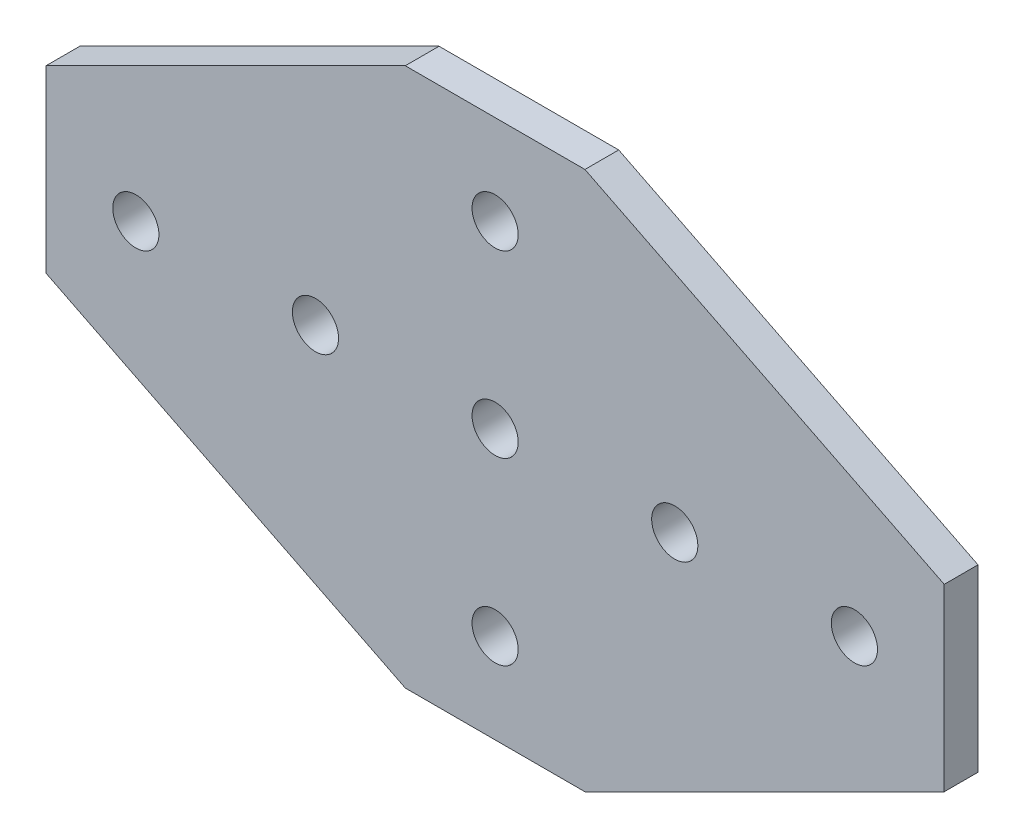
SolidWorks part; units mm, degrees
ref_plane "Front"
ref_plane "Top"
ref_plane "Right"
sketch "Sketch1" plane through (0, 0, 0) normal (0, 0, 1) x (1, 0, 0)
  line L0 (50.8, 0) -> (76.2, 0)
  line L1 (76.2, 0) -> (127, 25.4)
  line L2 (127, 25.4) -> (127, 50.8)
  line L3 (127, 50.8) -> (76.2, 76.2)
  line L4 (76.2, 76.2) -> (50.8, 76.2)
  line L5 (50.8, 76.2) -> (0, 50.8)
  line L6 (0, 50.8) -> (0, 25.4)
  line L7 (0, 25.4) -> (50.8, 0)
  line L8 (63.5, 76.2) -> (63.5, 0) construction
  line L9 (0, 38.1) -> (127, 38.1) construction
  dimension "WidthX" = 127
  dimension "HeightY" = 76.2
  dimension "CornerY" = 25.4
  dimension "CornerX" = 25.4
extrude "Base Extrude" add sketch "Sketch1" along normal blind 4.7752
sketch "Sketch2" plane through (0, 0, 4.7752) normal (0, 0, 1) x (1, 0, 0)
  line L0 (0, 50.8) -> (0, 25.4) construction
  line L1 (50.8, 0) -> (76.2, 0) construction
  circle A0 centre (12.7, 38.1) radius 3.2639
  dimension "Hole1Diam" = 6.5278
  dimension "Hole1X" = 12.7
  dimension "Hole1Y" = 38.1
extrude "Hole1" cut sketch "Sketch2" against normal through all
pattern_linear "Hole1 Pattern" count 5 spacing 25.4 along (1, 0, 0) of "Hole1"
sketch "Sketch3" plane through (0, 0, 4.7752) normal (0, 0, 1) x (1, 0, 0)
  line L0 (0, 50.8) -> (0, 25.4) construction
  line L1 (50.8, 0) -> (76.2, 0) construction
  circle A0 centre (63.5, 12.7) radius 3.2639
  dimension "Hole2Diam" = 6.5278
  dimension "Hole2X" = 63.5
  dimension "Hole2Y" = 12.7
extrude "Hole2" cut sketch "Sketch3" against normal through all
pattern_linear "Hole2 Pattern" count 2 spacing 50.8 along (0, 1, 0) count 2 spacing 50.8 along (0, 1, 0) of "Hole2"
ref_plane "Mate 1"
ref_plane "Mate 2"
ref_plane "Mate 3"
ref_plane "Mate 4"
ref_plane "Mate 5"
ref_plane "Mate 6"
ref_plane "Mate 7"
ref_plane "Mate 8"
ref_plane "Mate 9"
ref_plane "Mate 10"
ref_plane "Mate 11"
ref_plane "Mate 12"
ref_plane "Mate 13"
ref_plane "Mate 14"
ref_plane "Plane1"
ref_plane "Plane2"
ref_plane "Plane3"
ref_plane "Plane4"
ref_plane "Plane5"
ref_plane "Plane6"
ref_plane "Plane7"
ref_plane "Plane8"
